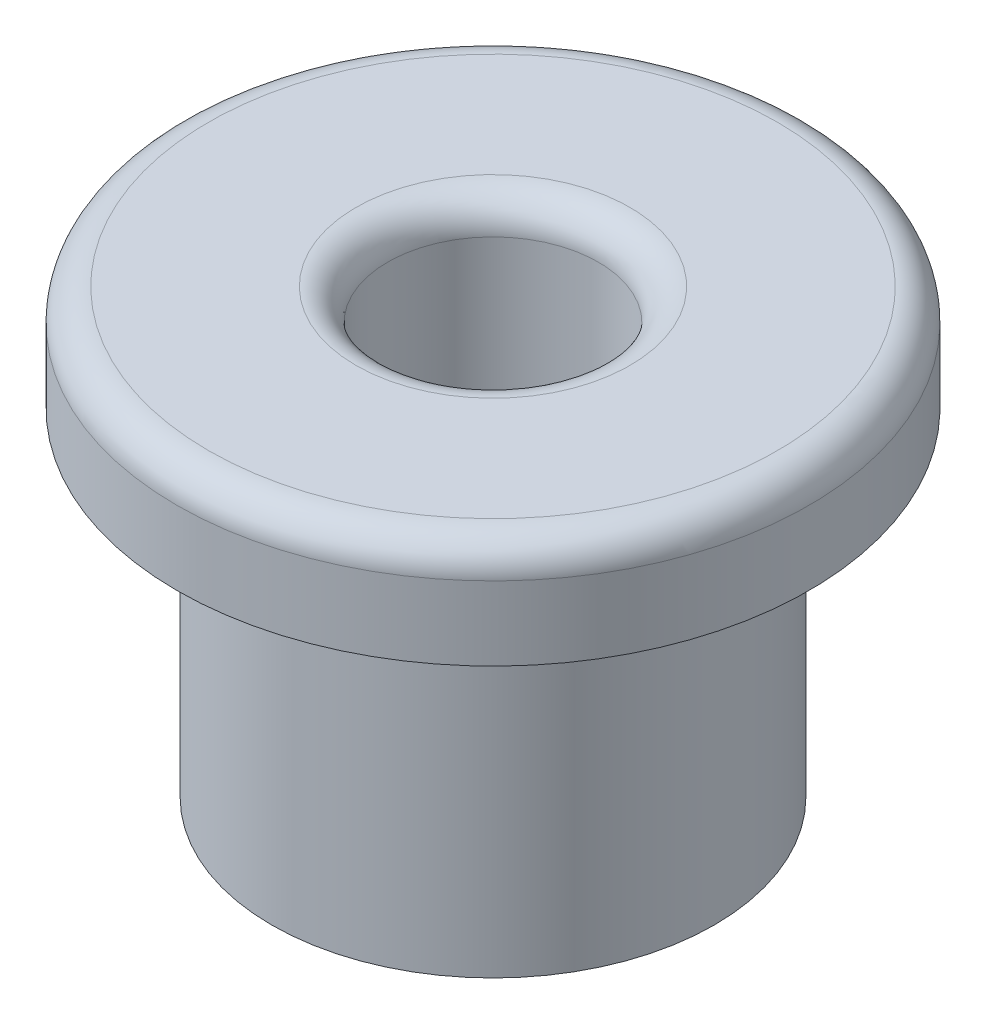
SolidWorks part; units mm, degrees
ref_plane "前视基准面" through (0, 0, 0) normal (0, 0, 1) x (1, 0, 0)
ref_plane "上视基准面" through (0, 0, 0) normal (0, 1, 0) x (1, 0, 0)
ref_plane "右视基准面" through (0, 0, 0) normal (1, 0, 0) x (0, 0, -1)
sketch "草图1" plane through (0, 0, 0) normal (0, 1, 0) x (1, 0, 0)
  circle A0 centre (0, 0) radius 2.1
  circle A1 centre (0, 0) radius 1
extrude "凸台-拉伸1" add sketch "草图1" along normal blind 4.2 contours A0 A1
sketch "草图2" plane through (0, 4.2, 0) normal (0, 1, 0) x (1, 0, 0)
  circle A0 centre (0, 0) radius 3
  circle A1 centre (0, 0) radius 2.1
  circle M2 centre (0, 0) radius 2.1
extrude "凸台-拉伸3" add sketch "草图2" against normal blind 1 contours A0 M2
fillet "圆角1" radius 0.3 2 edges at (0, 4.2, 3) (0, 4.2, 1)
